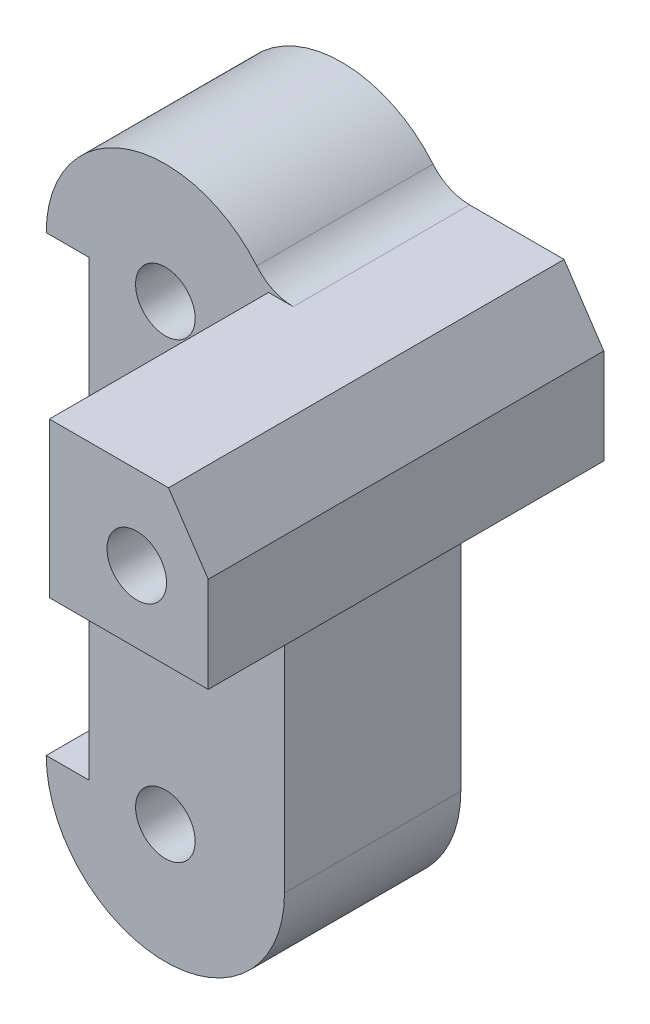
SolidWorks part; units mm, degrees
ref_plane "前视基准面" through (0, 0, 0) normal (0, 0, 1) x (1, 0, 0)
ref_plane "上视基准面" through (0, 0, 0) normal (0, 1, 0) x (1, 0, 0)
ref_plane "右视基准面" through (0, 0, 0) normal (1, 0, 0) x (0, 0, -1)
sketch "草图1" plane through (0, 0, 0) normal (0, 0, 1) x (1, 0, 0)
  line L0 (-3.2, 19) -> (-3.2, 0)
  line L1 (-3.2, 0) -> (-5, 0)
  line L2 (0, -5) -> (7.6941, -5) construction
  line L6 (5, 4) -> (5, 15)
  line L7 (-3.2, 19) -> (-5, 19)
  line L8 (-3.2, 9.5) -> (6.6148, 9.5) construction
  line L9 (4.3333, 21.4944) -> (9.3333, 21.4944)
  line L10 (9.3333, 21.4944) -> (11, 19)
  line L11 (11, 19) -> (11, 15)
  line L12 (11, 15) -> (5, 15)
  line L13 (5, 4) -> (5, 0)
  line L14 (0, 19) -> (0, 0) construction
  arc A0 (-5, 0) -> (4.4101, -2.356) centre (0, 0) ccw construction
  arc A1 (4.3333, 21.4944) -> (-5, 19) centre (0, 19) ccw
  arc A2 (-5, 0) -> (5, 0) centre (0, 0) ccw
  dimension "D1" = 5
  dimension "D4" = 5
  dimension "D2" = 1.8
  dimension "D3" = 19
  dimension "D5" = 9.5
  dimension "D6" = 20
  dimension "D7" = 6
  dimension "D8" = 3
  dimension "D9" = 4
  dimension "D10" = 5
extrude "凸台-拉伸1" add sketch "草图1" along normal blind 7.4
sketch "草图2" plane through (0, 0, 7.4) normal (0, 0, 1) x (1, 0, 0)
  line L1 (9.3333, 21.4944) -> (4.3333, 21.4944) construction
  line L4 (11, 19) -> (9.3333, 21.4944) construction
  line L5 (11, 15) -> (11, 19) construction
  line L6 (5, 15) -> (11, 15) construction
  line L7 (9.3333, 21.4944) -> (4.3333, 21.4944)
  line L8 (11, 19) -> (9.3333, 21.4944)
  line L9 (11, 15) -> (11, 19)
  line L10 (-3.2, 9.5) -> (13.3258, 9.5) construction
  line L11 (-3.2, 19) -> (-3.2, 0) construction
  line L12 (5, 15) -> (11, 15)
  line L13 (4.3333, 21.4944) -> (4.3333, 15)
  line L14 (4.3333, 15) -> (5, 15)
extrude "凸台-拉伸2" add sketch "草图2" along normal blind 9.2
sketch "草图3" plane through (0, 0, 7.4) normal (0, 0, 1) x (1, 0, 0)
  line L0 (0, 0) -> (0, 23.2652) construction
  circle A0 centre (0, 0) radius 1.5 construction
  circle A1 centre (0, 19) radius 1.5 construction
  dimension "D1" = 3
  dimension "D2" = 3
sketch "草图5" plane through (-3.2, 0, 0) normal (-1, 0, 0) x (0, 0, 1)
  line L0 (4.4, 20) -> (4.4, 0) construction
  line L3 (7.4, 19) -> (0, 19) construction
  line L4 (7.4, 19) -> (7.4, 0) construction
  circle A0 centre (4.4, 5) radius 1.5 construction
  circle A1 centre (4.4, 15) radius 1.5 construction
  dimension "D1" = 3
  dimension "D2" = 4
  dimension "D3" = 10
  dimension "D4" = 3
hole_wizard "M3 螺纹孔1" positions "3D草图1" profile "草图6" tap size "M3" standard "GB"
sketch3d "3D草图1"
  point P0 (-3.2, 15, 4.4)
  point P3 (-3.2, 5, 4.4)
sketch "草图6" plane through (-3.2, 15, 4.4) normal (0, 1, 0) x (0, 0, 1)
  line L0 (0, 0) -> (0, 7.2511)
  line L1 (0, 7.2511) -> (1.25, 6.5)
  line L2 (1.25, 6.5) -> (1.25, 0)
  line L5 (1.25, 0) -> (0, 0)
  line L10 (0, 7.2511) -> (-1.25, 6.5) construction
  line L11 (0, -6.35) -> (0, 107.95) construction
  dimension "螺纹孔钻头直径" = 2.5
  dimension "螺纹孔钻头深度" = 6.5
  dimension "导头角度" = 118
cosmetic thread "孔螺蚊线1" parameters "D1"=4, "D2"=3
cosmetic thread "孔螺蚊线2" parameters "D1"=4, "D2"=3
hole_wizard "M3 螺纹孔3" positions "3D草图3" profile "草图8" tap size "M3" standard "GB" end condition through all
sketch3d "3D草图3"
  point P0 (0, 0, 7.4)
  point P3 (0, 19, 7.4)
sketch "草图8" plane through (0, 0, 7.4) normal (1, 0, 0) x (0, -1, 0)
  line L0 (0, 0) -> (0, 7.4)
  line L1 (0, 7.4) -> (1.25, 7.4)
  line L2 (1.25, 7.4) -> (1.25, 0)
  line L5 (1.25, 0) -> (0, 0)
  line L11 (0, -6.35) -> (0, 107.95) construction
  dimension "通孔螺纹孔钻头直径" = 2.5
  dimension "通孔螺纹孔钻头深度" = 7.4
cosmetic thread "孔螺蚊线3" parameters "D2"=3
cosmetic thread "孔螺蚊线4" parameters "D2"=3
fillet "圆角1" radius 2 1 edges at (4.3333, 21.4944, 3.7)
ref_plane "基准面1" through (0, 13.5, 0) normal (0, 1, 0) x (1, 0, 0)
sketch "草图10" plane through (0, 13.5, 0) normal (0, 1, 0) x (1, 0, 0)
  line L0 (-3.2, -7.4) -> (-0.3716, -7.4)
  line L1 (-0.3716, -7.4) -> (-3.2, -4.5716)
  line L2 (-3.2, -4.5716) -> (-3.2, -7.4)
  line L3 (-3.2, -7.4) -> (-5, -7.4) construction
  line L4 (-3.2, -7.4) -> (-5, -7.4) construction
  line L5 (-3.2, -7.4) -> (-5, -7.4) construction
  dimension "D1" = 4
extrude "切除-拉伸1" cut sketch "草图10" against normal blind 5
sketch "草图11" plane through (0, 0, 16.6) normal (0, 0, 1) x (1, 0, 0)
  line L0 (4.3333, 15) -> (11, 15) construction
  circle A0 centre (8, 18) radius 1.5 construction
  dimension "D1" = 3
  dimension "D2" = 3
  dimension "D3" = 8
hole_wizard "M3 螺纹孔5" positions "3D草图5" profile "草图12" tap size "M3" standard "GB" end condition through all
sketch3d "3D草图5"
  point P0 (8, 18, 16.6)
sketch "草图12" plane through (8, 18, 16.6) normal (1, 0, 0) x (0, -1, 0)
  line L0 (0, 0) -> (0, 16.6)
  line L1 (0, 16.6) -> (1.25, 16.6)
  line L2 (1.25, 16.6) -> (1.25, 0)
  line L5 (1.25, 0) -> (0, 0)
  line L11 (0, -6.35) -> (0, 107.95) construction
  dimension "通孔螺纹孔钻头直径" = 2.5
  dimension "通孔螺纹孔钻头深度" = 16.6
cosmetic thread "孔螺蚊线7" parameters "D2"=3
